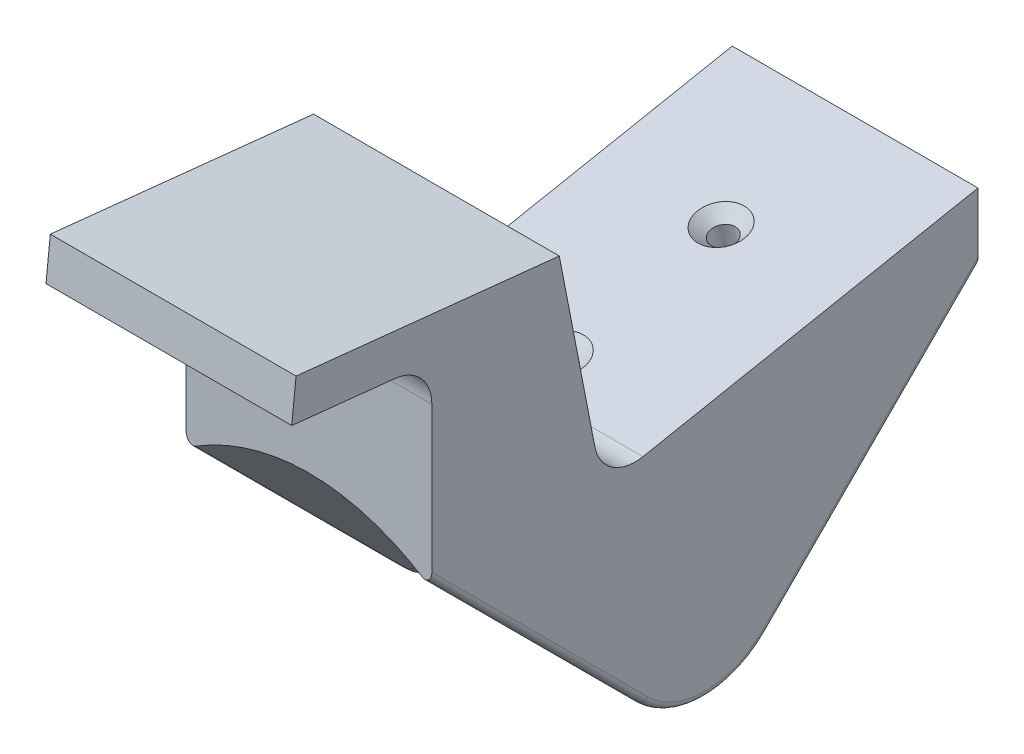
SolidWorks part; units mm, degrees
material "vespel"
ref_plane "Front Plane" through (0, 0, 0) normal (0, 0, 1) x (1, 0, 0)
ref_plane "Top Plane" through (0, 0, 0) normal (0, 1, 0) x (1, 0, 0)
ref_plane "Right Plane" through (0, 0, 0) normal (1, 0, 0) x (0, 0, -1)
sketch "Sketch1" plane through (0, 0, 0) normal (1, 0, 0) x (0, 0, -1)
  line L0 (3.0052, -3.0052) -> (20, 13.9896)
  line L1 (0, 30) -> (20, 30)
  line L2 (0, 0) -> (0, -4.25) construction
  line L3 (0, 0) -> (2.9486, 0) construction
  line L4 (3.0052, 8.9031) -> (3.0052, -10.7555) construction
  line L5 (20, 30) -> (20, 13.9896)
  line L6 (0, 30) -> (0, -4.25)
  arc A0 (0, -4.25) -> (3.0052, -3.0052) centre (0, 0) ccw
  point P14 (0, 30)
  dimension "D1" = 8.5
  dimension "D2" = 30
  dimension "D3" = 45
  dimension "D4" = 20
extrude "Boss-Extrude1" add sketch "Sketch1" along normal mid plane 18
sketch "Sketch2" plane through (0, 0, 0) normal (1, 0, 0) x (0, 0, -1)
  line L0 (3.0052, -3.0052) -> (20, 13.9896) construction
  line L1 (3.0052, -3.0052) -> (20, 13.9896)
  arc A0 (0, -4.25) -> (3.0052, -3.0052) centre (0, 0) ccw construction
  arc A1 (0, -4.25) -> (3.0052, -3.0052) centre (0, 0) ccw
sketch "Sketch3" plane through (0, 0, 0) normal (0, 0, 1) x (1, 0, 0)
  line L0 (9, -4.25) -> (-9, -4.25) construction
  line L1 (9, -4.25) -> (-9, -4.25)
  line L2 (0, 0) -> (0, 23.6164) construction
  line L3 (-11.3012, -4.65) -> (15.1743, -4.65) construction
  line L4 (-9, -4.25) -> (-9, -6.7012)
  line L5 (9, -4.25) -> (9, -6.7012)
  line L6 (-9, 30) -> (-9, -4.25) construction
  arc A0 (9, -6.7012) -> (-9, -6.7012) centre (0, -25.42) ccw
  dimension "D1" = 41.54
  dimension "D2" = 0.4
sweep "Sweep1" add profiles "Sketch3" path "Sketch2"
sketch "Sketch4" plane through (0, 0, -20) normal (0, 0, -1) x (-1, 0, 0)
  line L0 (9, 13.9896) -> (9, 30) construction
  line L1 (-9, 30) -> (9, 30)
  line L2 (-9, 30) -> (-9, -14.3136)
  line L3 (-9, -14.3136) -> (9, -14.3136)
  line L4 (9, 30) -> (9, -14.3136)
extrude "Cut-Extrude3" cut sketch "Sketch4" along normal blind 6
fillet "Fillet1" radius 0.5 4 edges at (9, 2.8923, -12.3692) (-9, 2.8923, -12.3692) (9, -6.1911, -2.5644) (-9, -6.1911, -2.5644)
mirror "Mirror1" about plane through (9, 30, 0) normal (0, 0, -1) of bodies 103
sketch "Sketch5" plane through (0, 0, 0) normal (1, 0, 0) x (0, 0, -1)
  line L0 (20, 16) -> (-7.4856, 10.6573)
  line L1 (-11.2454, 30) -> (20, 30)
  line L2 (20, 30) -> (20, 16)
  line L3 (20, 11.6247) -> (20, 30) construction
  line L4 (20, 30) -> (-20, 30) construction
  line L5 (-11.2454, 30) -> (-7.4856, 10.6573)
  dimension "D1" = 14
  dimension "D2" = 11
  dimension "D3" = 28
extrude "Cut-Extrude4" cut sketch "Sketch5" against normal mid plane 40
hole_wizard "#2-56 Tapped Hole1" positions "Sketch7" profile "Sketch6" tap size "#2-56" standard "ANSI Inch"
sketch "Sketch7" plane through (0, 11.6714, 2.2687) normal (0, 0.9816, 0.1908) x (1, 0, 0)
  line L0 (0, 0) -> (0, 7.9549) construction
  line L1 (-9, 22.6855) -> (9, 22.6855) construction
  point P0 (0, 12.6855)
  point P5 (0, 22.6855)
  point P8 (0, 0.6855)
  dimension "D1" = 10
  dimension "D2" = 12
sketch "Sketch6" plane through (0, 14.0919, -10.1837) normal (1, 0, 0) x (0, -0.1908, 0.9816)
  line L0 (0, 0) -> (0, 7.1742)
  line L1 (0, 7.1742) -> (0.889, 6.64)
  line L2 (0.889, 6.64) -> (0.889, 0.8382)
  line L3 (0.889, 0.8382) -> (1.7272, 0)
  line L5 (1.7272, 0) -> (0, 0)
  line L6 (-0.889, 0.8382) -> (-1.7272, 0) construction
  line L10 (0, 7.1742) -> (-0.889, 6.64) construction
  line L11 (0, -6.35) -> (0, 107.95) construction
  dimension "Tap Drill Dia." = 1.778
  dimension "Tap Drill Depth" = 6.64
  dimension "Near C'Sink Dia." = 3.4544
  dimension "Near C'Sink Angle" = 90
  dimension "Drill Angle" = 118
cosmetic thread "Hole Thread1" parameters "D1"=4.37, "D2"=2.1844
cosmetic thread "Hole Thread2" parameters "D1"=4.37, "D2"=2.1844
sketch "Sketch8" plane through (-9, 0, 0) normal (-1, 0, 0) x (0, 0, 1)
  line L0 (10.6659, 27.019) -> (20, 28)
  line L1 (11.2454, 30) -> (7.4856, 10.6573) construction
  line L2 (20, 11.6247) -> (20, 30) construction
  line L3 (20, 28) -> (20, 30)
  line L4 (20, 30) -> (11.2454, 30)
  line L5 (11.2454, 30) -> (10.6659, 27.019)
  dimension "D1" = 2
  dimension "D2" = 6
extrude "Cut-Extrude5" cut sketch "Sketch8" against normal through all
sketch "Sketch10" plane through (-9, 0, 0) normal (-1, 0, 0) x (0, 0, 1)
  line L0 (20, 28) -> (29.9452, 29.0453)
  line L1 (29.9452, 29.0453) -> (30.2588, 26.0617)
  line L2 (30.2588, 26.0617) -> (20, 24.9835)
  line L3 (20, 11.6247) -> (20, 28) construction
  line L4 (20, 28) -> (20, 24.9835)
  line L5 (10.6659, 27.019) -> (20, 28) construction
  dimension "D1" = 3
  dimension "D2" = 10
extrude "Boss-Extrude2" add sketch "Sketch10" against normal up to surface (18 mm away) up to face at (9, 11.852, 2.2689)
fillet "Fillet2" radius 3 2 edges at (0, 10.6573, 7.4856)
